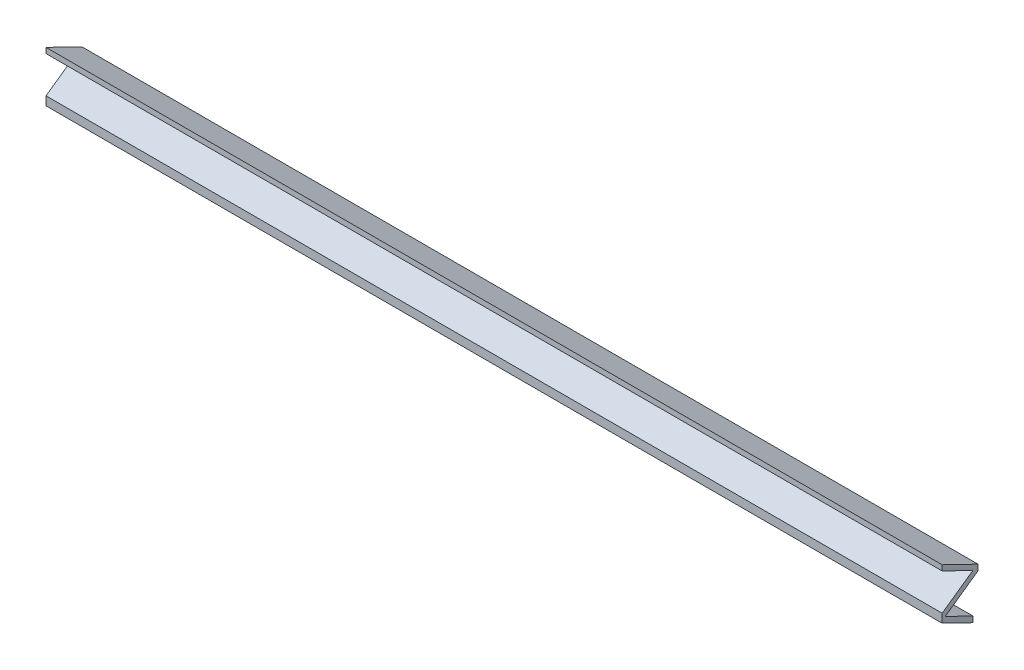
SolidWorks part; units mm, degrees
ref_plane "Front Plane" through (0, 0, 0) normal (0, 0, 1) x (1, 0, 0)
ref_plane "Top Plane" through (0, 0, 0) normal (0, 1, 0) x (1, 0, 0)
ref_plane "Right Plane" through (0, 0, 0) normal (1, 0, 0) x (0, 0, -1)
sketch "Sketch2" plane through (0, 0, 0) normal (1, 0, 0) x (0, 0, -1)
  line L0 (0, 0) -> (0, -3)
  line L1 (0, -3) -> (17.1502, -11.3188)
  line L4 (0, -23.3977) -> (0, -28.2555)
  line L6 (0, -23.3977) -> (17.1502, -11.3188)
  line L7 (20, -12.9365) -> (1.6979, -25.8266)
  line L9 (1.6979, -25.8266) -> (17.1502, -33.3218)
  line L11 (17.1502, -36.5743) -> (0, -28.2555)
  line L12 (0, -25.8266) -> (1.6979, -25.8266) construction
  line L13 (20, -11.3188) -> (17.1502, -11.3188) construction
  line L14 (17.1502, -33.3218) -> (17.1502, -36.5743)
  line L34 (0, 0) -> (20, -9.7011)
  line L35 (20, -9.7011) -> (20, -12.9365)
  point P6 (14.6866, -21.0334)
  point P7 (18.7448, -14.4674)
  point P8 (16.3182, -32.8544)
  point P11 (0, 0)
  point P12 (1.4612, -23.4376)
  point P13 (17.1502, -33.2461)
  point P14 (0, -25.8266)
  dimension "D1" = 3
  dimension "D4" = 20
extrude "Boss-Extrude1" add sketch "Sketch2" along normal blind 500
